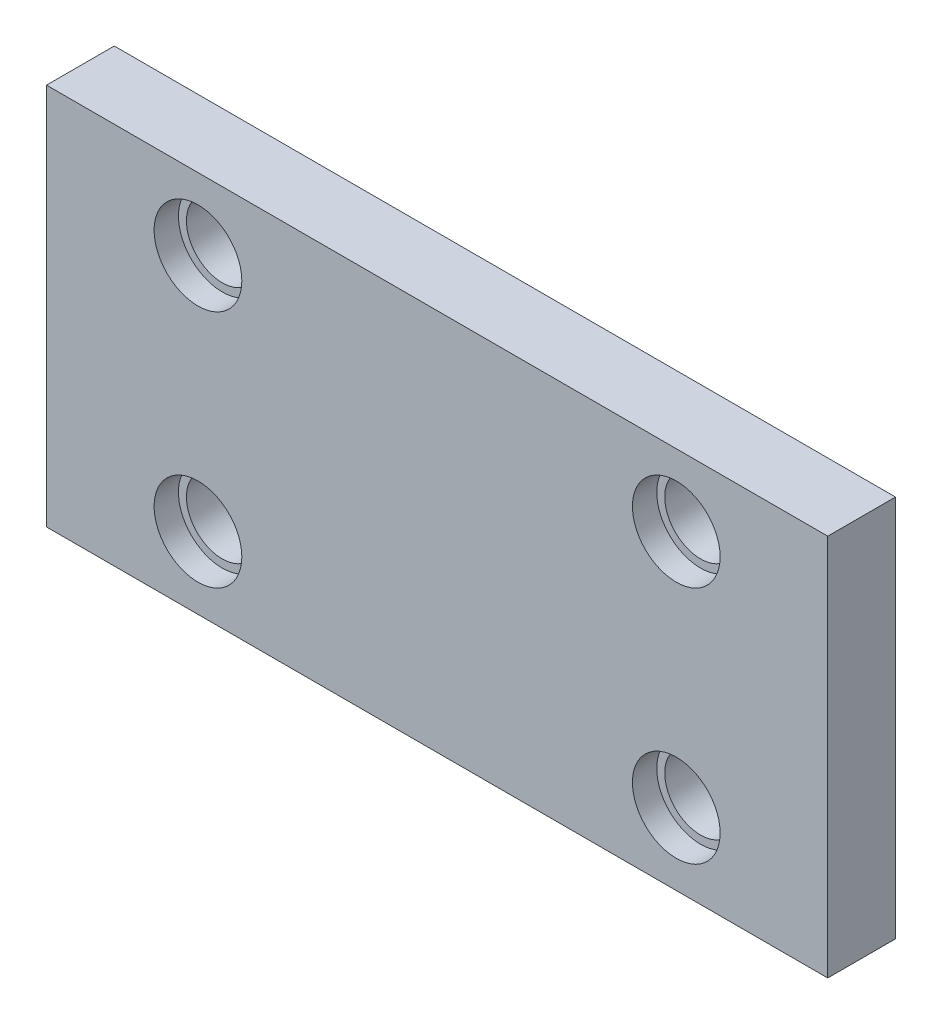
SolidWorks part; units mm, degrees
ref_plane "Front Plane" through (0, 0, 0) normal (0, 0, 1) x (1, 0, 0)
ref_plane "Top Plane" through (0, 0, 0) normal (0, 1, 0) x (1, 0, 0)
ref_plane "Right Plane" through (0, 0, 0) normal (1, 0, 0) x (0, 0, -1)
sketch "Sketch1" plane through (0, 0, 0) normal (0, 0, 1) x (1, 0, 0)
  line L1 (98, -48) -> (-98, -48)
  line L2 (98, -48) -> (98, 48)
  line L3 (98, 48) -> (-98, 48)
  line L4 (-98, -48) -> (-98, 48)
  line L5 (98, -48) -> (-98, 48) construction
  line L6 (98, 48) -> (-98, -48) construction
  point P0 (0, 0)
extrude "Extrude1" add sketch "Sketch1" against normal blind 17
hole_wizard "CBORE for 14 mm Locating Guide Bushing1" positions "Sketch3" profile "Sketch2" counterbore size "14" standard "HASCO Metric" end condition through all
sketch "Sketch3" plane through (49.2461, -1.0958, 0) normal (0, 0, -1) x (-1, 0, 0)
  point P0 (-10.7539, 31.0958)
  point P5 (109.2461, 31.0958)
  point P8 (109.2461, -28.9042)
  point P11 (-10.7539, -28.9042)
sketch "Sketch2" plane through (60, 30, 0) normal (1, 0, 0) x (0, -1, 0)
  line L0 (0, 0) -> (0, 17)
  line L1 (0, 17) -> (9, 17)
  line L3 (9, 17) -> (9, 6.1)
  line L4 (9, 6.1) -> (11, 6.1)
  line L5 (11, 6.1) -> (11, 0)
  line L7 (11, 0) -> (0, 0)
  line L11 (0, -6.35) -> (0, 107.95) construction
  dimension "Диаметр сквозного отверстия" = 18
  dimension "Глубина сквозного отверстия" = 17
  dimension "Диаметр цековки" = 22
  dimension "Глубина цековки" = 6.1
